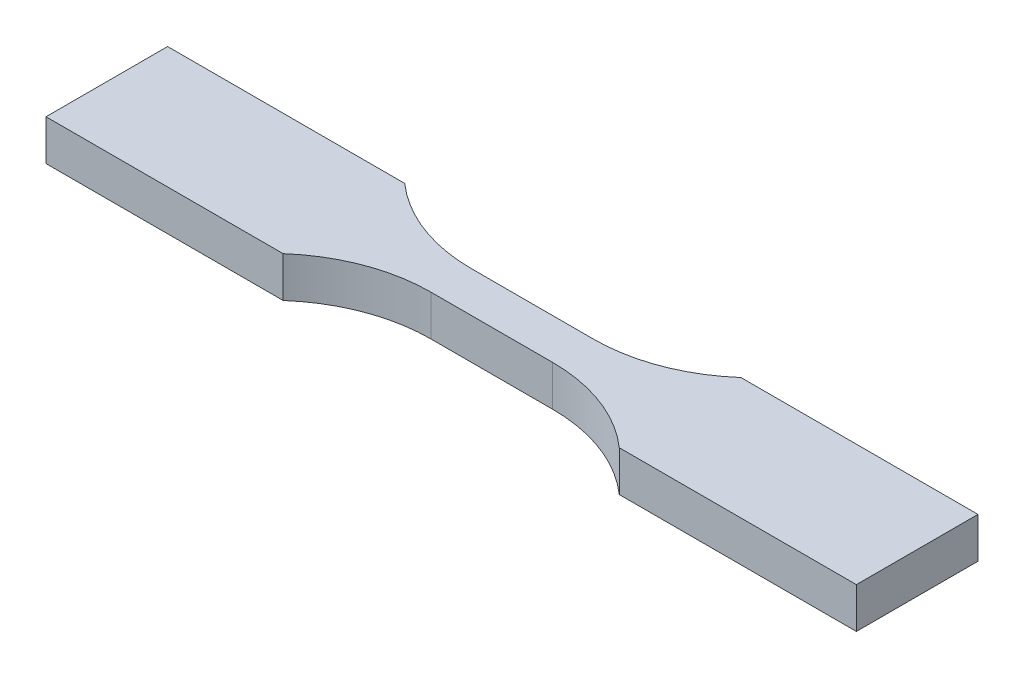
SolidWorks part; units mm, degrees
ref_plane "Alzado" through (0, 0, 0) normal (0, 0, 1) x (1, 0, 0)
ref_plane "Planta" through (0, 0, 0) normal (0, 1, 0) x (1, 0, 0)
ref_plane "Vista lateral" through (0, 0, 0) normal (1, 0, 0) x (0, 0, -1)
sketch "Croquis1" plane through (0, 0, 0) normal (0, 1, 0) x (1, 0, 0)
  line L0 (-4.765, 1.5942) -> (4.765, 1.5942)
  line L1 (-4.765, -1.5858) -> (4.765, -1.5858)
  line L2 (13.17, 4.765) -> (31.75, 4.765)
  line L3 (31.75, 4.765) -> (31.75, -4.765)
  line L4 (31.75, -4.765) -> (13.17, -4.765)
  line L5 (-13.17, 4.765) -> (-31.75, 4.765)
  line L6 (-31.75, 4.765) -> (-31.75, -4.765)
  line L7 (-31.75, -4.765) -> (-13.17, -4.765)
  line L8 (13.17, -4.765) -> (-13.17, -4.765) construction
  arc A0 (-4.765, 1.5942) -> (-13.17, 4.765) centre (-4.7745, 14.2942) cw
  arc A3 (-4.765, -1.5858) -> (-13.17, -4.765) centre (-4.765, -14.2858) ccw
  arc A4 (4.765, 1.5942) -> (13.17, 4.765) centre (4.7745, 14.2942) ccw
  arc A5 (4.765, -1.5858) -> (13.17, -4.765) centre (4.765, -14.2858) cw
  point P4 (0, -1.5858)
  point P5 (0, 1.5942)
  point P9 (31.75, 0)
  point P17 (0, -4.765)
  dimension "D2" = 12.7
  dimension "D1" = 3.18
  dimension "D3" = 9.53
  dimension "D4" = 9.53
  dimension "D5" = 63.5
  dimension "D6" = 18.58
extrude "Saliente-Extruir1" add sketch "Croquis1" along normal blind 3.18
